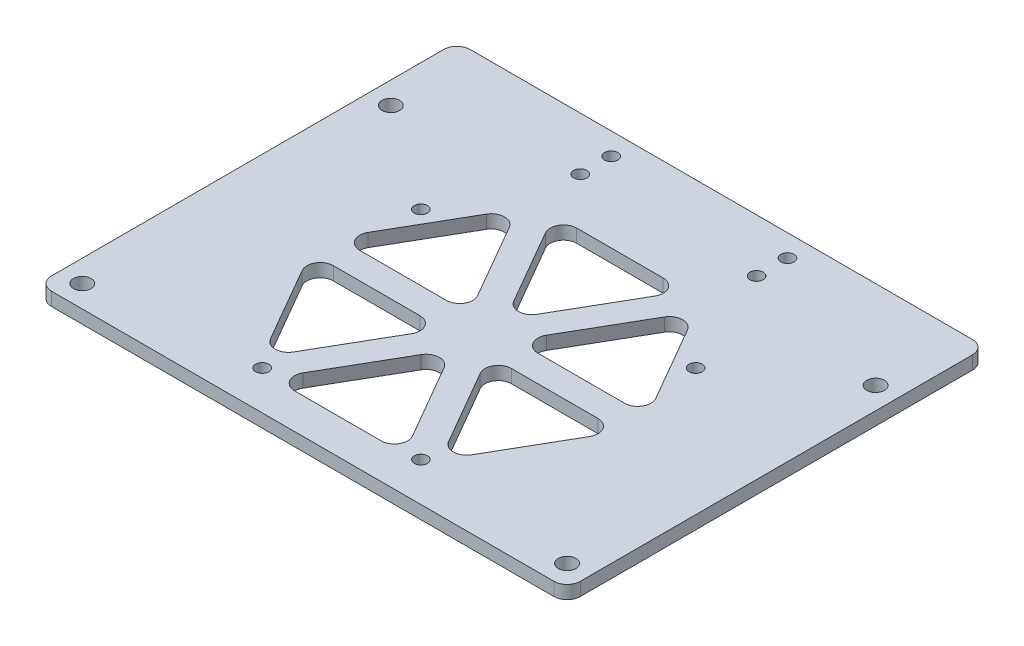
SolidWorks part; units mm, degrees
material "7075-T6，板材(SS)"
ref_plane "前视基准面" through (0, 0, 0) normal (0, 0, 1) x (1, 0, 0)
ref_plane "上视基准面" through (0, 0, 0) normal (0, 1, 0) x (1, 0, 0)
ref_plane "右视基准面" through (0, 0, 0) normal (1, 0, 0) x (0, 0, -1)
sketch "草图1" plane through (0, 0, 0) normal (0, 1, 0) x (1, 0, 0)
  line L1 (-60, -40) -> (60, -40)
  line L2 (-60, -40) -> (-60, 40)
  line L3 (-60, 40) -> (60, 40)
  line L4 (60, -40) -> (60, 40)
  line L5 (-60, -40) -> (60, 40) construction
  line L6 (-60, 40) -> (60, -40) construction
  point P0 (0, 0)
  dimension "D1" = 120
  dimension "D2" = 80
extrude "凸台-拉伸1" add sketch "草图1" along normal blind 3
sketch "草图3" plane through (0, 3, 0) normal (0, 1, 0) x (1, 0, 0)
  line L0 (0, 0) -> (0, 18) construction
  line L1 (-31.1769, 18) -> (31.1769, 18) construction
  line L2 (0, 0) -> (0, -31.1769) construction
  line L3 (-18, -31.1769) -> (18, -31.1769) construction
  circle A0 centre (0, 0) radius 36 construction
  circle A1 centre (-31.1769, 18) radius 1.5
  circle A2 centre (31.1769, 18) radius 1.5
  circle A3 centre (-18, -31.1769) radius 1.5
  circle A4 centre (18, -31.1769) radius 1.5
  point P7 (0, 18)
  point P12 (0, -31.1769)
  dimension "D1" = 72
  dimension "D3" = 3
  dimension "D2" = 18
  dimension "D4" = 18
extrude "切除-拉伸2" cut sketch "草图3" against normal through all
sketch "草图4" plane through (0, 3, 0) normal (0, 1, 0) x (1, 0, 0)
  line L1 (-55, -35) -> (55, -35) construction
  line L2 (-55, -35) -> (-55, 35) construction
  line L3 (-55, 35) -> (55, 35) construction
  line L4 (55, -35) -> (55, 35) construction
  line L5 (-55, -35) -> (55, 35) construction
  line L6 (-55, 35) -> (55, -35) construction
  circle A0 centre (-55, 35) radius 2
  circle A1 centre (55, 35) radius 2
  circle A2 centre (55, -35) radius 2
  circle A3 centre (-55, -35) radius 2
  point P0 (0, 0)
  dimension "D3" = 4
  dimension "D1" = 110
  dimension "D2" = 70
extrude "切除-拉伸3" cut sketch "草图4" against normal through all
sketch "草图5" plane through (0, 0, -40) normal (0, 0, -1) x (-1, 0, 0)
  line L1 (-60, 0) -> (60, 0)
  line L2 (-60, 0) -> (-60, 3)
  line L3 (-60, 3) -> (60, 3)
  line L4 (60, 0) -> (60, 3)
extrude "凸台-拉伸2" add sketch "草图5" along normal blind 15
sketch "草图6" plane through (0, 3, 0) normal (0, 1, 0) x (1, 0, 0)
  line L0 (20.2073, 35) -> (-20.2073, -35) construction
  line L1 (20.2073, -35) -> (40.4145, 0)
  line L2 (40.4145, 0) -> (20.2073, 35)
  line L3 (20.2073, 35) -> (-20.2073, 35)
  line L4 (-20.2073, 35) -> (-40.4145, 0)
  line L5 (-40.4145, 0) -> (-20.2073, -35)
  line L6 (-20.2073, -35) -> (20.2073, -35)
  line L7 (-20.2073, 35) -> (20.2073, -35) construction
  line L8 (-40.4145, 0) -> (40.4145, 0) construction
  line L9 (-22.8053, 33.5) -> (17.6092, -36.5)
  line L10 (17.6092, 36.5) -> (-22.8053, -33.5)
  line L11 (-40.4145, -3) -> (40.4145, -3)
  line L12 (-17.6092, 36.5) -> (22.8053, -33.5)
  line L13 (22.8053, 33.5) -> (-17.6092, -36.5)
  line L14 (-40.4145, 3) -> (40.4145, 3)
  line L15 (18.4752, -32) -> (36.9504, 0)
  line L16 (36.9504, 0) -> (18.4752, 32)
  line L17 (18.4752, 32) -> (-18.4752, 32)
  line L18 (-18.4752, 32) -> (-36.9504, 0)
  line L19 (-36.9504, 0) -> (-18.4752, -32)
  line L20 (-18.4752, -32) -> (18.4752, -32)
  circle A0 centre (0, 0) radius 35 construction
  dimension "D1" = 70
  dimension "D2" = 3
  dimension "D3" = 3
  dimension "D4" = 3
extrude "切除-拉伸4" cut sketch "草图6" against normal blind 15 contours L10 L17 L12 | L14 L16 L13 | L12 L15 L11 | L13 L20 L9 | L11 L19 L10 | L9 L18 L14
fillet "圆角1" radius 3 18 edges at (5.1962, 1.5, -3) (20.2073, 1.5, -29) (35.2184, 1.5, -3) (35.2184, 1.5, 3) (5.1962, 1.5, 3) (20.2073, 1.5, 29) (15.0111, 1.5, 32) (0, 1.5, 6) (-15.0111, 1.5, 32) (-20.2073, 1.5, 29) (-35.2184, 1.5, 3) (-5.1962, 1.5, 3) (-5.1962, 1.5, -3) (-35.2184, 1.5, -3) (-20.2073, 1.5, -29) (15.0111, 1.5, -32) (0, 1.5, -6) (-15.0111, 1.5, -32)
sketch "草图7" plane through (0, 3, 0) normal (0, 1, 0) x (1, 0, 0)
  line L0 (0, 55) -> (0, 50) construction
  line L1 (-60, 55) -> (60, 55) construction
  line L2 (20, 50) -> (-20, 50) construction
  line L4 (-20, 50) -> (20, 50) construction
  line L5 (-20, 50) -> (-20, 43) construction
  line L6 (-20, 43) -> (20, 43) construction
  line L7 (20, 50) -> (20, 43) construction
  circle A0 centre (-20, 50) radius 1.5
  circle A1 centre (20, 50) radius 1.5
  circle A2 centre (-20, 43) radius 1.5
  circle A3 centre (20, 43) radius 1.5
  point P8 (0, 50)
  dimension "D3" = 3
  dimension "D4" = 7
  dimension "D1" = 5
  dimension "D2" = 40
extrude "切除-拉伸5" cut sketch "草图7" against normal through all
fillet "圆角2" radius 3 4 edges at (60, 1.5, 40) (-60, 1.5, 40) (-60, 1.5, -55) (60, 1.5, -55)
